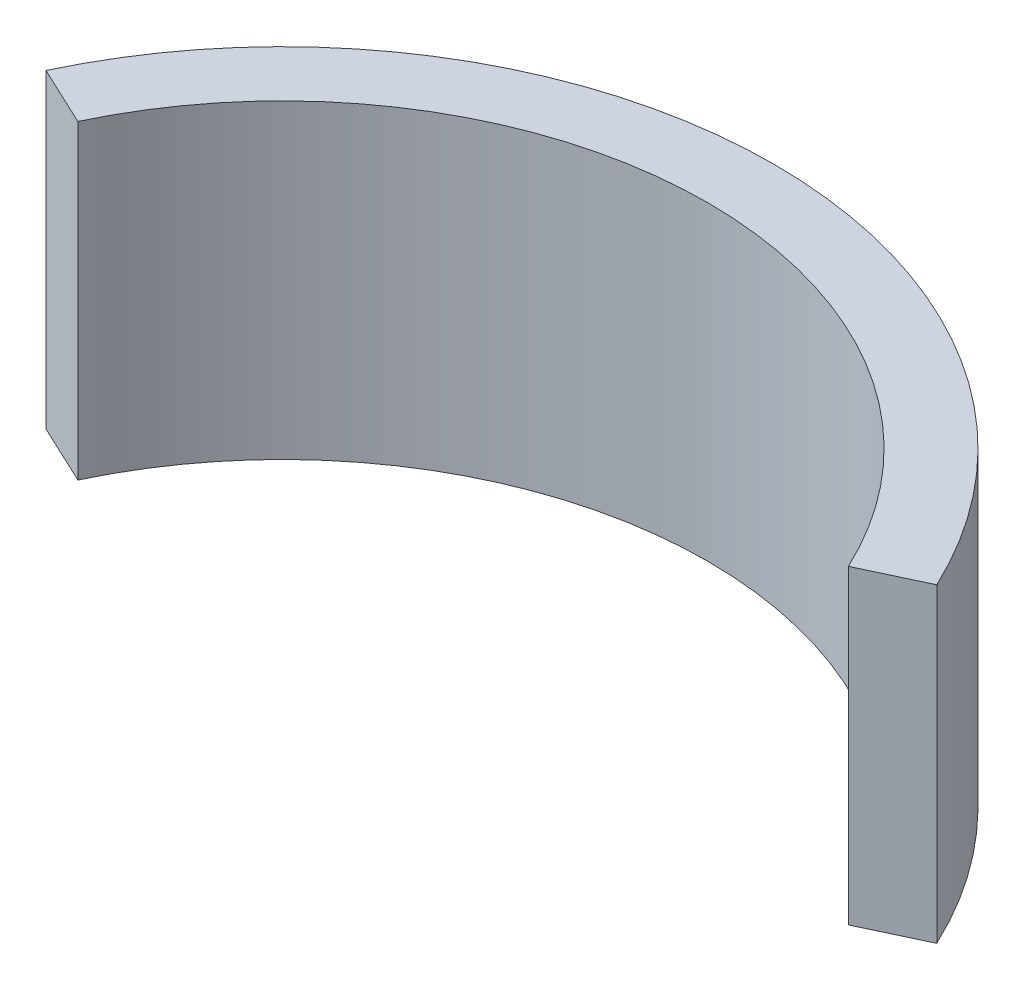
SolidWorks part; units mm, degrees
ref_plane "Front Plane" through (0, 0, 0) normal (0, 0, 1) x (1, 0, 0)
ref_plane "Top Plane" through (0, 0, 0) normal (0, 1, 0) x (1, 0, 0)
ref_plane "Right Plane" through (0, 0, 0) normal (1, 0, 0) x (0, 0, -1)
sketch "Sketch1" plane through (0, 0, 0) normal (0, 1, 0) x (1, 0, 0)
  line L0 (7.5433, -6.0894) -> (8.7198, -5.5364)
  line L1 (-8.7198, -5.5364) -> (-7.5433, -6.0894)
  arc A0 (7.5433, -6.0894) -> (-7.5433, -6.0894) centre (0, -9.635) ccw
  arc A1 (8.7198, -5.5364) -> (-8.7198, -5.5364) centre (0, -9.635) ccw
  dimension "D1" = 8.335
  dimension "D2" = 9.635
  dimension "D3" = 7.5433
  dimension "D4" = 5.5364
extrude "Boss-Extrude1" add sketch "Sketch1" along normal blind 6.08
